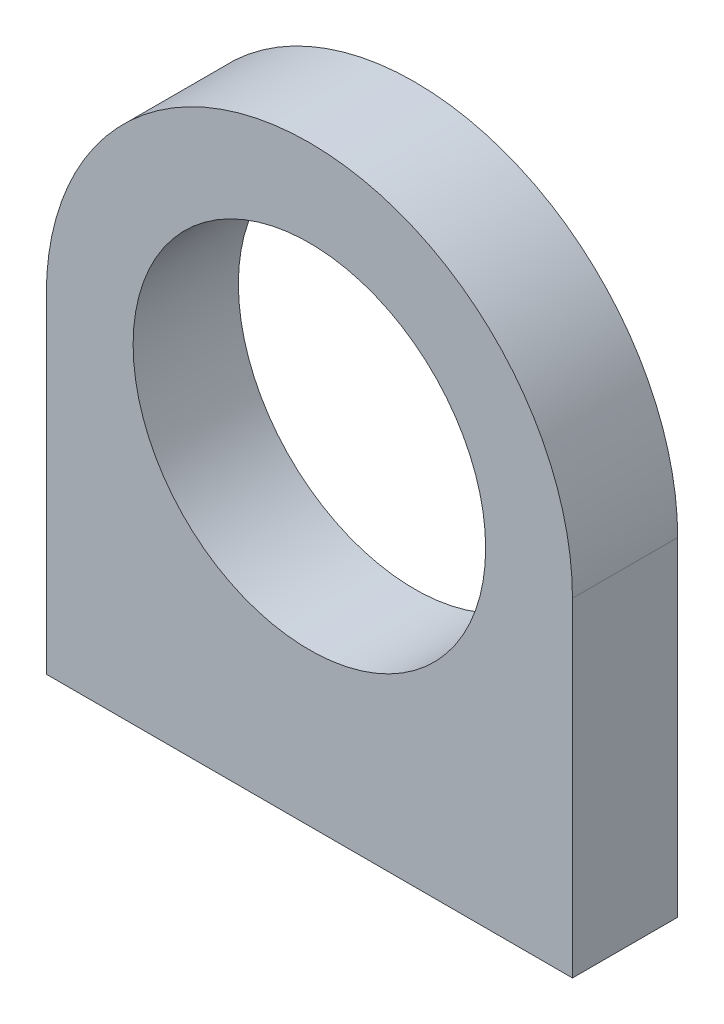
SolidWorks part; units mm, degrees
ref_plane "Plan de face" through (0, 0, 0) normal (0, 0, 1) x (1, 0, 0)
ref_plane "Plan de dessus" through (0, 0, 0) normal (0, 1, 0) x (1, 0, 0)
ref_plane "Plan de droite" through (0, 0, 0) normal (1, 0, 0) x (0, 0, -1)
sketch "Esquisse1" plane through (0, 0, 0) normal (0, 0, 1) x (1, 0, 0)
  line L0 (0, 0) -> (0, 10) construction
  line L1 (-20, 0) -> (20, 0) construction
  line L2 (-20, 0) -> (-20, -25)
  line L3 (-20, -25) -> (20, -25)
  line L4 (20, 0) -> (20, -25)
  circle A0 centre (0, 0) radius 20 construction
  arc A1 (-20, 0) -> (20, 0) centre (0, 0) cw
  circle A2 centre (0, 0) radius 7
  circle A3 centre (0, 10) radius 1.8
  circle A4 centre (10, 0) radius 1.8
  circle A5 centre (0, -10) radius 1.8
  circle A6 centre (-10, 0) radius 1.8
  point P20 (0, 0)
  dimension "D3" = 14
  dimension "D5" = 3.6
  dimension "D1" = 40
  dimension "D2" = 25
  dimension "D4" = 10
  dimension "D6" = 4
extrude "Boss.-Extru.1" add sketch "Esquisse1" along normal blind 8
sketch "Esquisse2" plane through (0, 0, 8) normal (0, 0, 1) x (1, 0, 0)
  circle A0 centre (0, 0) radius 13.4
  dimension "D1" = 26.8
extrude "Enlèv. mat.-Extru.1" cut sketch "Esquisse2" against normal through all
sketch "Esquisse3" plane through (0, -25, 0) normal (0, -1, 0) x (1, 0, 0)
  line L0 (-15, 4) -> (15, 4) construction
  line L1 (0, 0) -> (0, 8) construction
  line L2 (-20, 8) -> (20, 8) construction
  line L3 (-20, 8) -> (-20, 0) construction
  circle A0 centre (-15, 4) radius 2
  circle A1 centre (15, 4) radius 2
  point P8 (0, 4)
  point P9 (0, 4)
  dimension "D1" = 4
  dimension "D2" = 5
extrude "Enlèv. mat.-Extru.2" cut sketch "Esquisse3" against normal blind 12
chamfer "Chanfrein1" distance 1 angle 45 2 edges at (15, -25, 2) (-15, -25, 2)
